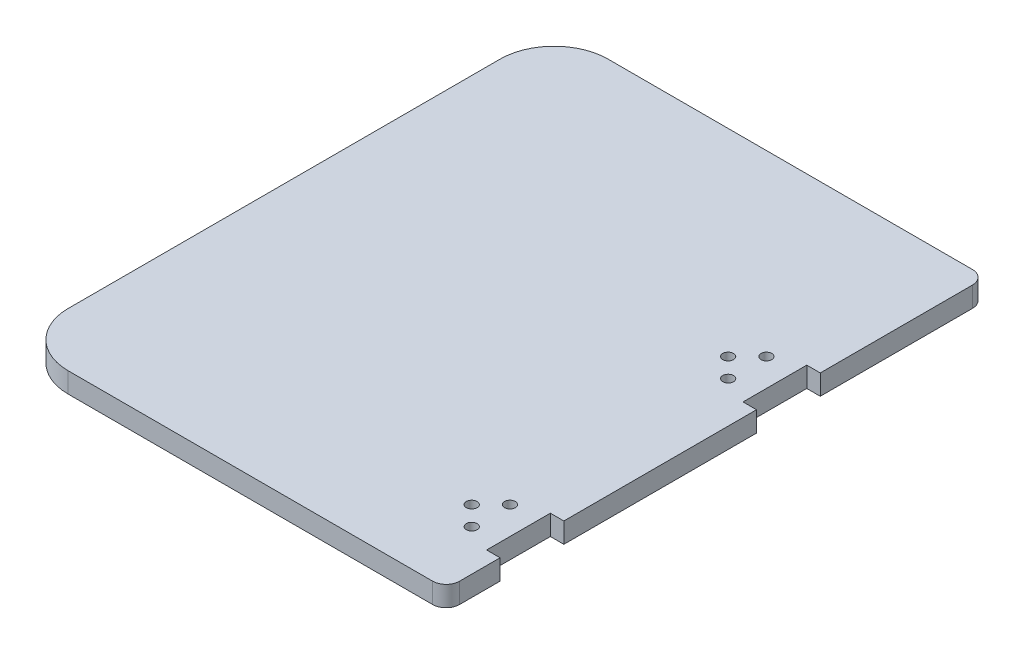
SolidWorks part; units mm, degrees
ref_plane "Front Plane" through (0, 0, 0) normal (0, 0, 1) x (1, 0, 0)
ref_plane "Top Plane" through (0, 0, 0) normal (0, 1, 0) x (1, 0, 0)
ref_plane "Right Plane" through (0, 0, 0) normal (1, 0, 0) x (0, 0, -1)
sketch "Sketch1" plane through (0, 0, 0) normal (0, 1, 0) x (1, 0, 0)
  line L1 (25.4, 0) -> (196.85, 0)
  line L2 (0, 25.4) -> (0, 228.6)
  line L3 (25.4, 254) -> (196.85, 254)
  line L4 (203.2, 6.35) -> (203.2, 247.65)
  arc A0 (25.4, 254) -> (0, 228.6) centre (25.4, 228.6) ccw
  arc A1 (25.4, 0) -> (0, 25.4) centre (25.4, 25.4) cw
  arc A2 (196.85, 0) -> (203.2, 6.35) centre (196.85, 6.35) ccw
  arc A3 (203.2, 247.65) -> (196.85, 254) centre (196.85, 247.65) ccw
  point P7 (0, 254)
  point P10 (0, 0)
  point P15 (203.2, 254)
  dimension "D3" = 25.4
  dimension "D4" = 6.35
  dimension "D1" = 203.2
  dimension "D2" = 254
extrude "Boss-Extrude1" add sketch "Sketch1" along normal blind 9.525
sketch "Sketch2" plane through (0, 9.525, 0) normal (0, 1, 0) x (1, 0, 0)
  line L0 (196.85, 55.4) -> (203.2, 55.4)
  line L1 (196.85, 55.4) -> (196.85, 25.4)
  line L2 (196.85, 25.4) -> (203.2, 25.4)
  line L3 (203.2, 55.4) -> (203.2, 25.4)
  line L4 (203.2, 40.4) -> (157.7993, 40.4) construction
  line L5 (203.2, 6.35) -> (203.2, 247.65) construction
  line L6 (25.4, 0) -> (196.85, 0) construction
  line L7 (196.85, 176.05) -> (203.2, 176.05)
  line L8 (196.85, 176.05) -> (196.85, 146.05)
  line L9 (196.85, 146.05) -> (203.2, 146.05)
  line L10 (203.2, 176.05) -> (203.2, 146.05)
  line L11 (203.2, 161.05) -> (157.7993, 161.05) construction
  circle A0 centre (174.85, 40.4) radius 2.54
  circle A1 centre (183.85, 49.4) radius 2.54
  circle A2 centre (183.85, 31.4) radius 2.54
  circle A3 centre (174.85, 161.05) radius 2.54
  circle A4 centre (183.85, 170.05) radius 2.54
  circle A5 centre (183.85, 152.05) radius 2.54
  dimension "D2" = 5.08
  dimension "D1" = 30
  dimension "D3" = 9
  dimension "D4" = 6.35
  dimension "D5" = 28.35
  dimension "D6" = 19.35
  dimension "D7" = 25.4
  dimension "D9" = 120.65
  dimension "D8" = 2
extrude "Cut-Extrude1" cut sketch "Sketch2" against normal up to next
